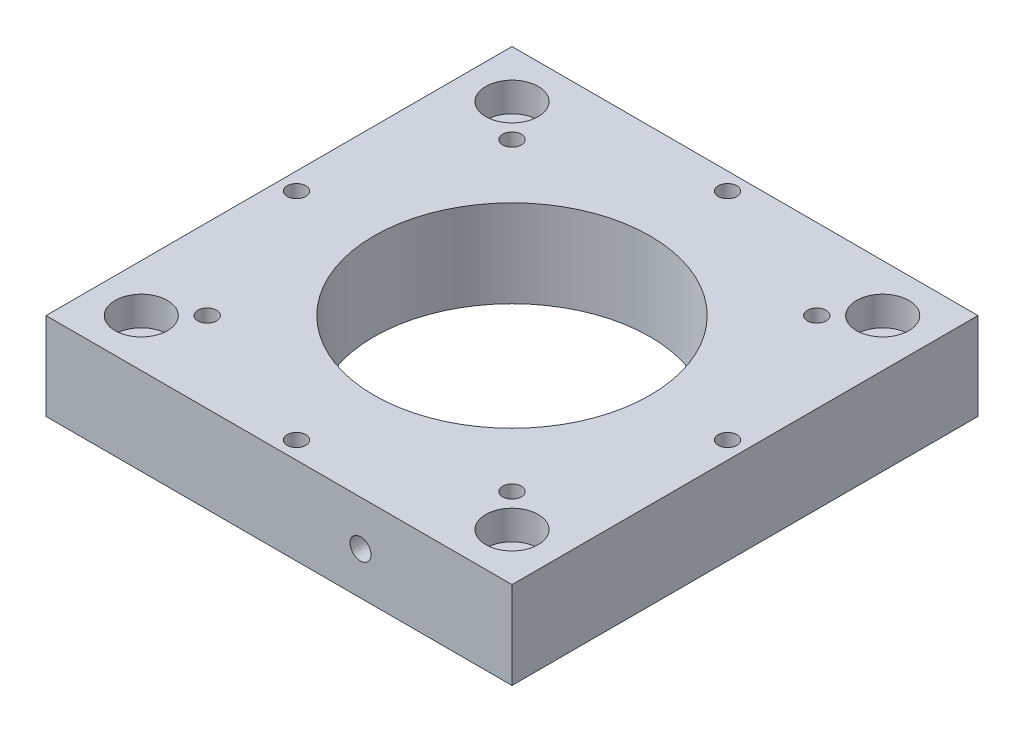
SolidWorks part; units mm, degrees
other "标注1"
sketch "草图20" plane through (-40, 128, 27.5) normal (-0.9349, 0.1755, 0.3084) x (0.3368, 0.1651, 0.927)
ref_plane "前视基准面" through (0, 0, 0) normal (0, 0, 1) x (1, 0, 0)
ref_plane "上视基准面" through (0, 0, 0) normal (0, 1, 0) x (1, 0, 0)
ref_plane "右视基准面" through (0, 0, 0) normal (1, 0, 0) x (0, 0, -1)
other "Configuration Table"
sketch "草图22" plane through (0, 0, 0) normal (0, 1, 0) x (1, 0, 0)
  line L1 (-40, 40) -> (40, 40)
  line L2 (-40, 40) -> (-40, -40)
  line L3 (-40, -40) -> (40, -40)
  line L4 (40, 40) -> (40, -40)
  circle A6 centre (0, 37) radius 1.6
  circle A7 centre (26.163, 26.163) radius 1.6
  circle A8 centre (37, 0) radius 1.6
  circle A9 centre (26.163, -26.163) radius 1.6
  circle A10 centre (0, -37) radius 1.6
  circle A11 centre (-26.163, -26.163) radius 1.6
  circle A12 centre (-37, 0) radius 1.6
  circle A13 centre (-26.163, 26.163) radius 1.6
  circle A14 centre (0, 0) radius 23.7
  circle A16 centre (-31.8198, 31.8198) radius 2.6
  circle A17 centre (-31.8198, -31.8198) radius 2.6
  circle A18 centre (31.8198, -31.8198) radius 2.6
  circle A19 centre (31.8198, 31.8198) radius 2.6
  point P19 (0, 0)
  point P33 (0, 0)
  point P43 (0, 0)
  dimension "D1" = 4
  dimension "D2" = 8
extrude "凸台-拉伸1" add sketch "草图22" along normal blind 15
sketch "草图24" plane through (0, 0, 0) normal (0, -1, 0) x (1, 0, 0)
  circle A0 centre (0, 37) radius 2.9
  circle A1 centre (26.163, 26.163) radius 2.9
  circle A2 centre (37, 0) radius 2.9
  circle A3 centre (26.163, -26.163) radius 2.9
  circle A4 centre (0, -37) radius 2.9
  circle A5 centre (-26.163, -26.163) radius 2.9
  circle A6 centre (-37, 0) radius 2.9
  circle A7 centre (-26.163, 26.163) radius 2.9
  point P20 (0, 0)
  dimension "D1" = 8
extrude "切除-拉伸2" cut sketch "草图24" against normal blind 5
sketch "草图26" plane through (0, 15, 0) normal (0, 1, 0) x (1, 0, 0)
  circle A0 centre (-31.8198, 31.8198) radius 4.5
  circle A1 centre (31.8198, 31.8198) radius 4.5
  circle A2 centre (31.8198, -31.8198) radius 4.5
  circle A3 centre (-31.8198, -31.8198) radius 4.5
  point P12 (0, 0)
  dimension "D1" = 4
extrude "切除-拉伸4" cut sketch "草图26" against normal blind 5
sketch "草图31" plane through (0, 0, 40) normal (0, 0, 1) x (1, 0, 0)
  circle A0 centre (13.9983, 7.3106) radius 1.8
extrude "切除-拉伸6" cut sketch "草图31" against normal blind 12
sketch "草图36" plane through (0, 0, -40) normal (0, 0, -1) x (-1, 0, 0)
  circle A0 centre (-16.5048, 7.3512) radius 1.8
extrude "切除-拉伸9" cut sketch "草图36" against normal blind 12
